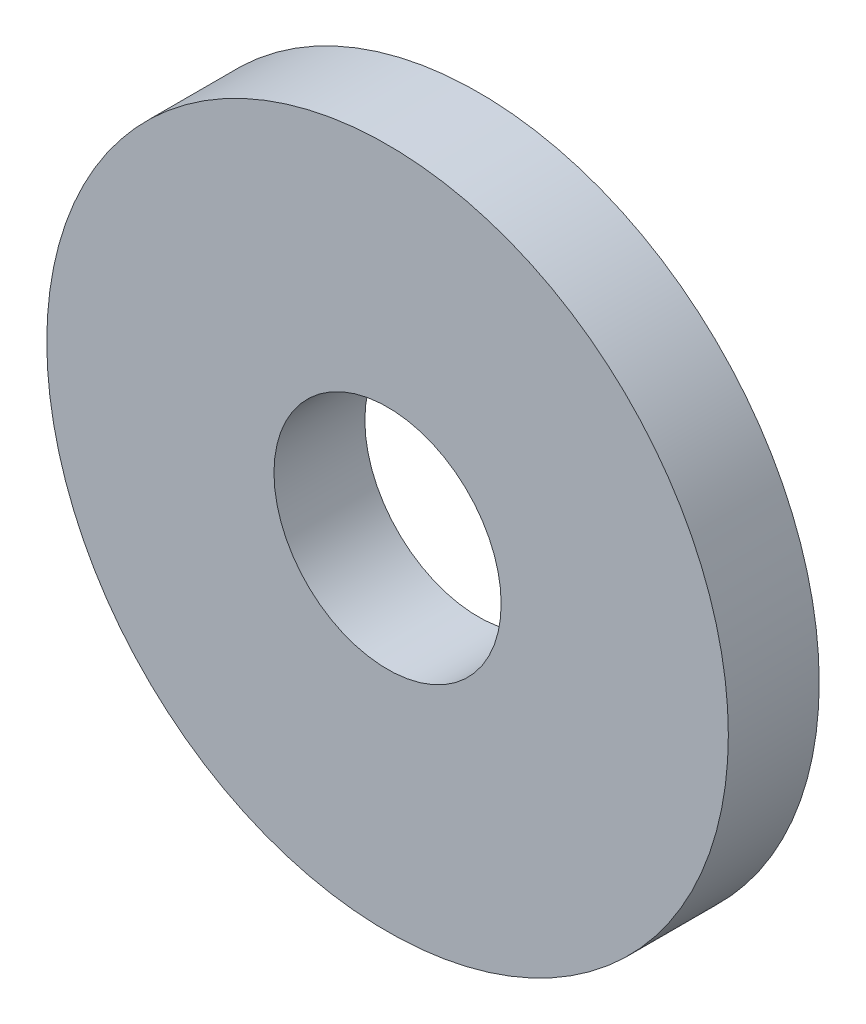
SolidWorks part; units mm, degrees
ref_plane "Plan de face" through (0, 0, 0) normal (0, 0, 1) x (1, 0, 0)
ref_plane "Plan de dessus" through (0, 0, 0) normal (0, 1, 0) x (1, 0, 0)
ref_plane "Plan de droite" through (0, 0, 0) normal (1, 0, 0) x (0, 0, -1)
sketch "Esquisse1" plane through (0, 0, 0) normal (0, 0, 1) x (1, 0, 0)
  circle A0 centre (0, 0) radius 4.5
  circle A1 centre (0, 0) radius 1.5
extrude "Extrusion1" add sketch "Esquisse1" along normal blind 1.2
